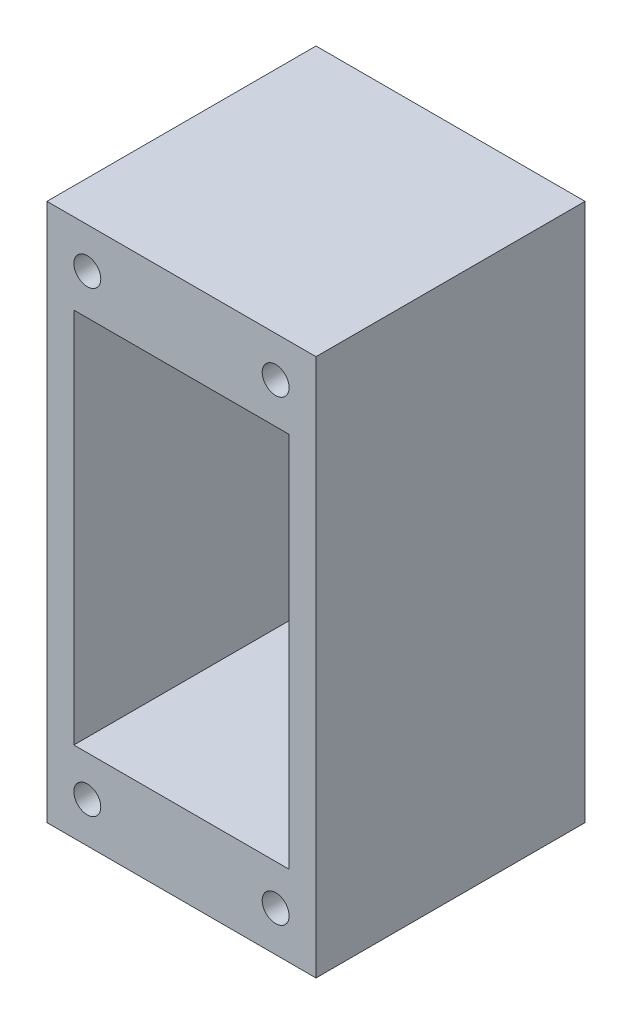
SolidWorks part; units mm, degrees
material "5052-H32"
ref_plane "Front Plane" through (0, 0, 0) normal (0, 0, 1) x (1, 0, 0)
ref_plane "Top Plane" through (0, 0, 0) normal (0, 1, 0) x (1, 0, 0)
ref_plane "Right Plane" through (0, 0, 0) normal (1, 0, 0) x (0, 0, -1)
sketch "Sketch1" plane through (0, 0, 0) normal (0, 0, 1) x (1, 0, 0)
  line L1 (-25, 50) -> (25, 50)
  line L2 (-25, 50) -> (-25, -50)
  line L3 (-25, -50) -> (25, -50)
  line L4 (25, 50) -> (25, -50)
  line L5 (-25, 50) -> (25, -50) construction
  line L6 (-25, -50) -> (25, 50) construction
  circle A0 centre (-17.5, 42.5) radius 2.5
  circle A1 centre (17.5, 42.5) radius 2.5
  circle A2 centre (-17.5, -42.5) radius 2.5
  circle A3 centre (17.5, -42.5) radius 2.5
  point P0 (0, 0)
  dimension "D3" = 5
  dimension "D4" = 5
  dimension "D5" = 5
  dimension "D6" = 5
  dimension "D1" = 50
  dimension "D2" = 100
  dimension "D7" = 7.5
  dimension "D8" = 7.5
  dimension "D9" = 7.5
  dimension "D10" = 7.5
  dimension "D11" = 7.5
  dimension "D12" = 7.5
  dimension "D13" = 7.5
  dimension "D14" = 7.5
extrude "Boss-Extrude1" add sketch "Sketch1" along normal blind 50
sketch "Sketch2" plane through (0, 0, 50) normal (0, 0, 1) x (1, 0, 0)
  line L0 (-20, 35) -> (20, 35)
  line L1 (20, 35) -> (20, -35)
  line L2 (20, -35) -> (-20, -35)
  line L3 (-20, -35) -> (-20, 35)
  line L4 (-25, 50) -> (-25, -50) construction
  line L5 (25, -50) -> (25, 50) construction
  line L6 (25, 50) -> (-25, 50) construction
  line L7 (-25, -50) -> (25, -50) construction
  dimension "D1" = 5
  dimension "D2" = 5
  dimension "D3" = 15
  dimension "D4" = 15
extrude "Cut-Extrude1" cut sketch "Sketch2" against normal blind 93
